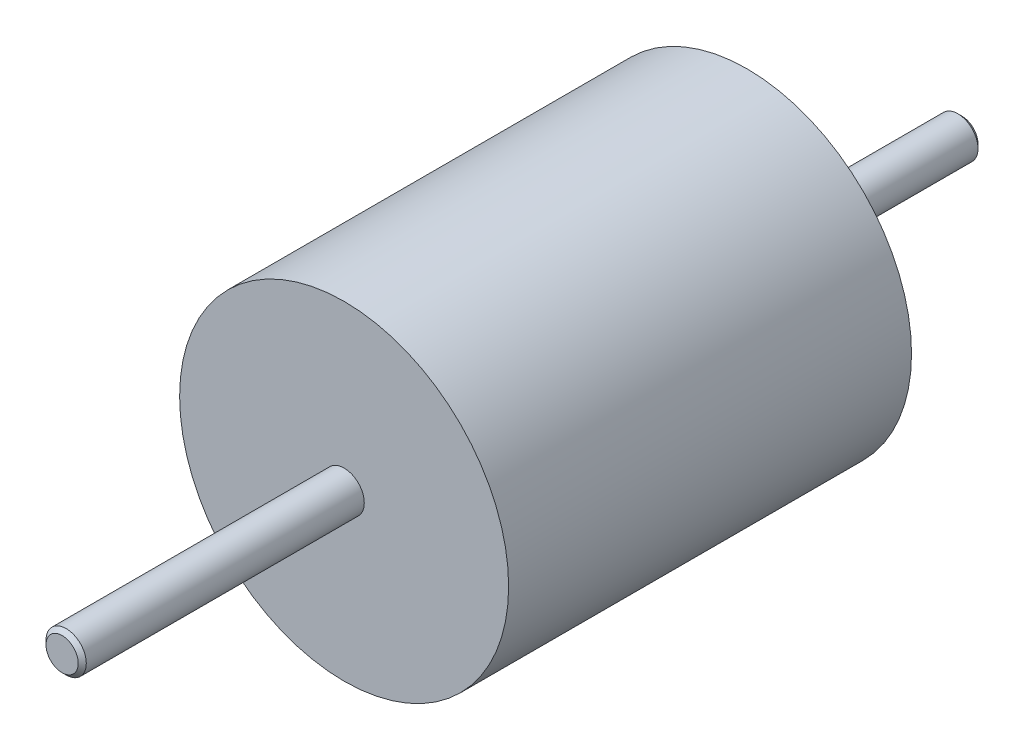
SolidWorks part; units mm, degrees
ref_plane "前视基准面" through (0, 0, 0) normal (0, 0, 1) x (1, 0, 0)
ref_plane "上视基准面" through (0, 0, 0) normal (0, 1, 0) x (1, 0, 0)
ref_plane "右视基准面" through (0, 0, 0) normal (1, 0, 0) x (0, 0, -1)
other "Configuration Table"
sketch "Sketch1" plane through (0, 0, 0) normal (0, 0, 1) x (1, 0, 0)
  circle A0 centre (0, 0) radius 1.5
  dimension "D1" = 3
extrude "Boss-Extrude1" add sketch "Sketch1" along normal mid plane 67
ref_plane "Plane1" through (0, 0, 12.5) normal (0, 0, 1) x (1, 0, 0)
sketch "Sketch2" plane through (0, 0, 12.5) normal (0, 0, 1) x (1, 0, 0)
  circle A0 centre (0, 0) radius 12.25
  circle A1 centre (0, 0) radius 1.5
  circle A2 centre (0, 0) radius 1.5
  dimension "D2" = 24.5
  dimension "D1" = 0
extrude "Boss-Extrude2" add sketch "Sketch2" against normal blind 30
chamfer "Chamfer1" distance 0.3 angle 45 2 edges at (1.5, 0, -33.5) (1.5, 0, 33.5)
